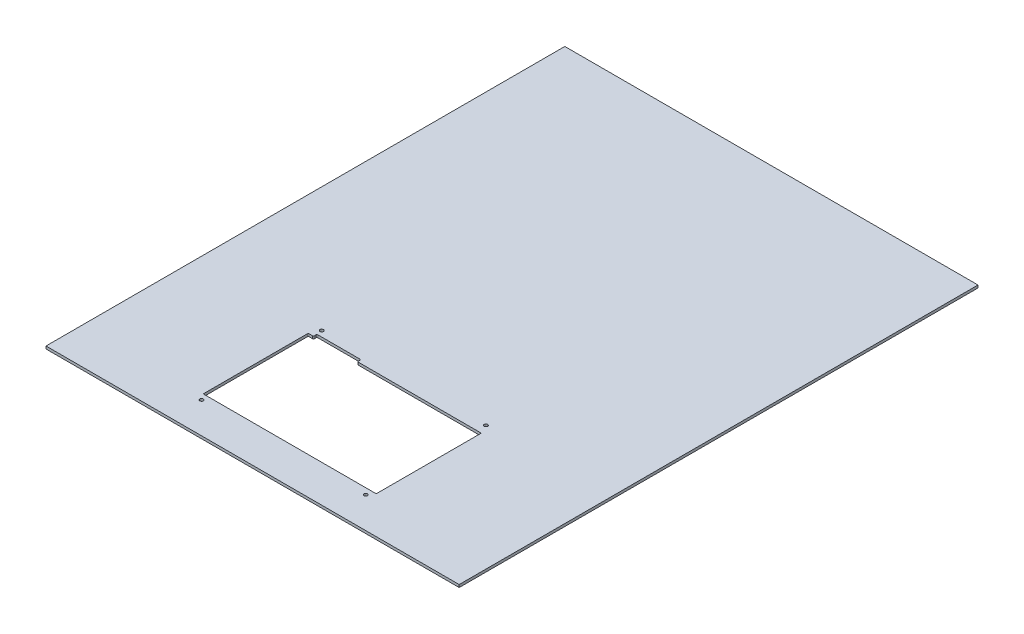
SolidWorks part; units mm, degrees
ref_plane "Front Plane" through (0, 0, 0) normal (0, 0, 1) x (1, 0, 0)
ref_plane "Top Plane" through (0, 0, 0) normal (0, 1, 0) x (1, 0, 0)
ref_plane "Right Plane" through (0, 0, 0) normal (1, 0, 0) x (0, 0, -1)
sketch "Sketch1" plane through (0, 0, 0) normal (0, 1, 0) x (1, 0, 0)
  line L1 (-197.5, -248) -> (197.5, -248)
  line L2 (-197.5, -248) -> (-197.5, 248)
  line L3 (-197.5, 248) -> (197.5, 248)
  line L4 (197.5, -248) -> (197.5, 248)
  line L5 (-197.5, -248) -> (197.5, 248) construction
  line L6 (-197.5, 248) -> (197.5, -248) construction
  point P0 (0, 0)
  dimension "D1" = 395
  dimension "D2" = 496
extrude "Boss-Extrude1" add sketch "Sketch1" along normal blind 2.5
sketch "Sketch4" plane through (0, 2.5, 0) normal (0, 1, 0) x (1, 0, 0)
  line L0 (0, -212.5) -> (0, -248) construction
  line L3 (-78.7, -112.1) -> (-82.2, -112.1)
  line L4 (82.2, -112.1) -> (-34.7, -112.1)
  line L5 (82.7, -112.6) -> (82.7, -212)
  line L6 (82.2, -212.5) -> (-82.2, -212.5)
  line L7 (-82.7, -112.6) -> (-82.7, -212)
  line L8 (82.7, -112.1) -> (-82.7, -212.5) construction
  line L9 (82.7, -212.5) -> (-82.7, -112.1) construction
  line L11 (-77.7, -111.1) -> (-77.7, -109.8)
  line L12 (-76.7, -108.8) -> (-36.7, -108.8)
  line L13 (-35.7, -111.1) -> (-35.7, -109.8)
  line L14 (-197.5, -248) -> (197.5, -248) construction
  arc A0 (-35.7, -111.1) -> (-34.7, -112.1) centre (-34.7, -111.1) ccw
  arc A1 (-35.7, -109.8) -> (-36.7, -108.8) centre (-36.7, -109.8) ccw
  arc A2 (-76.7, -108.8) -> (-77.7, -109.8) centre (-76.7, -109.8) ccw
  arc A3 (-78.7, -112.1) -> (-77.7, -111.1) centre (-78.7, -111.1) ccw
  arc A4 (82.7, -112.6) -> (82.2, -112.1) centre (82.2, -112.6) ccw
  arc A5 (-82.7, -112.6) -> (-82.2, -112.1) centre (-82.2, -112.6) cw
  arc A6 (-82.7, -212) -> (-82.2, -212.5) centre (-82.2, -212) ccw
  arc A7 (82.2, -212.5) -> (82.7, -212) centre (82.2, -212) ccw
  point P6 (0, -162.3)
  dimension "D7" = 1
  dimension "D8" = 0.5
  dimension "D6" = 42
  dimension "D1" = 3.3
  dimension "D2" = 165.4
  dimension "D3" = 100.4
  dimension "D4" = 5
  dimension "D5" = 35.5
extrude "Cut-Extrude1" cut sketch "Sketch4" against normal blind 2.5
sketch "Sketch6" plane through (0, 2.5, 0) normal (0, 1, 0) x (1, 0, 0)
  line L0 (78.5, -218.3) -> (-78.5, -218.3) construction
  line L1 (-78.5, -218.3) -> (-78.5, -103.4) construction
  line L2 (-78.5, -103.4) -> (78.5, -103.4) construction
  line L3 (78.5, -103.4) -> (78.5, -218.3) construction
  line L4 (-82.2, -212.5) -> (82.2, -212.5) construction
  line L6 (0, -212.5) -> (0, -218.3) construction
  line L7 (0, -218.3) -> (0, -248) construction
  line L8 (-197.5, -248) -> (197.5, -248) construction
  circle A4 centre (78.5, -103.4) radius 1.65
  circle A5 centre (-78.5, -103.4) radius 1.65
  circle A6 centre (-78.5, -218.3) radius 1.65
  circle A7 centre (78.5, -218.3) radius 1.65
  point P12 (0, -212.5)
  dimension "D1" = 3.3
  dimension "D2" = 3.3
  dimension "D3" = 3.3
  dimension "D4" = 3.3
  dimension "D5" = 114.9
  dimension "D6" = 157
  dimension "D7" = 5.8
  dimension "D8" = 78.5
extrude "Cut-Extrude2" cut sketch "Sketch6" against normal blind 2.5
equation "\"D2@Sketch6\"=\"D1@Sketch6\""
equation "\"D3@Sketch6\"=\"D2@Sketch6\""
equation "\"D4@Sketch6\"=\"D1@Sketch6\""
